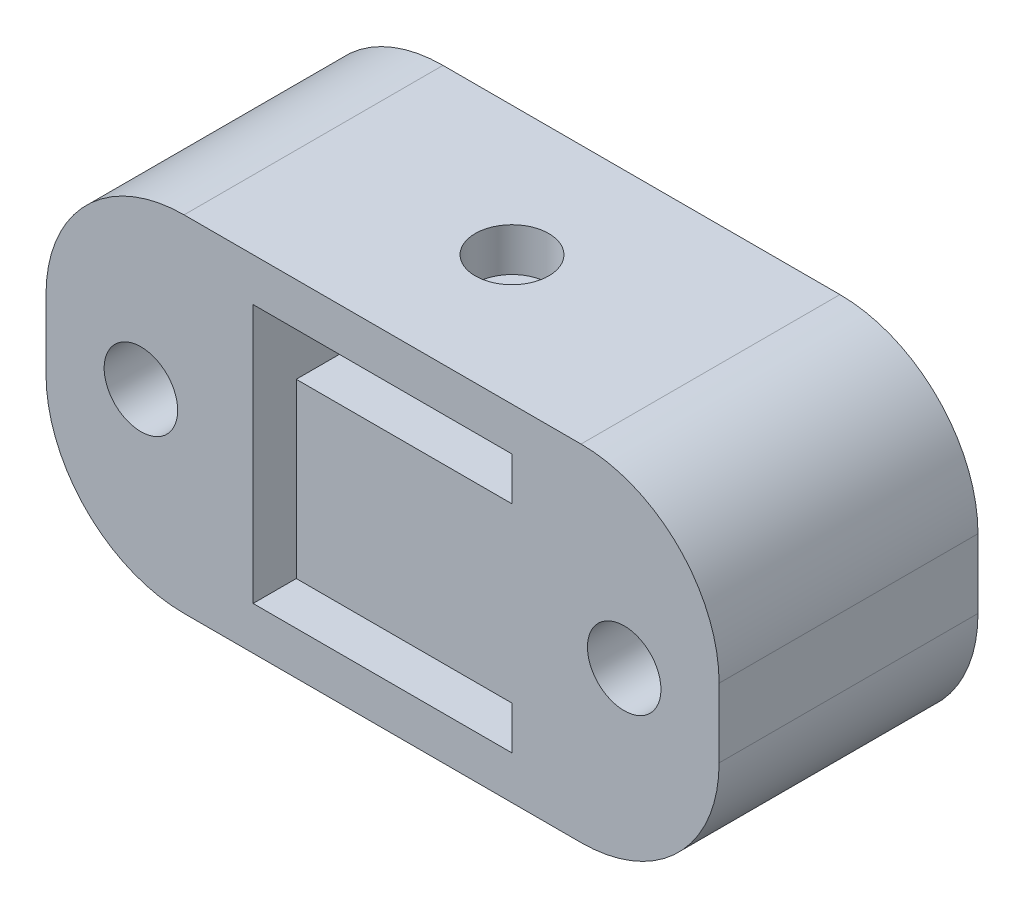
SolidWorks part; units mm, degrees
ref_plane "Front Plane" through (0, 0, 0) normal (0, 0, 1) x (1, 0, 0)
ref_plane "Top Plane" through (0, 0, 0) normal (0, 1, 0) x (1, 0, 0)
ref_plane "Right Plane" through (0, 0, 0) normal (1, 0, 0) x (0, 0, -1)
sketch "Sketch1" plane through (0, 0, 0) normal (0, 0, 1) x (1, 0, 0)
  line L1 (12.3825, -6.35) -> (-12.3825, -6.35)
  line L2 (12.3825, -6.35) -> (12.3825, 6.35)
  line L3 (12.3825, 6.35) -> (-12.3825, 6.35)
  line L4 (-12.3825, -6.35) -> (-12.3825, 6.35)
  line L5 (12.3825, -6.35) -> (-12.3825, 6.35) construction
  line L6 (12.3825, 6.35) -> (-12.3825, -6.35) construction
  point P0 (0, 0)
  dimension "D1" = 12.7
  dimension "D2" = 24.765
extrude "Boss-Extrude1" add sketch "Sketch1" along normal blind 9.525
sketch "Sketch2" plane through (0, 0, 9.525) normal (0, 0, 1) x (1, 0, 0)
  line L0 (4.7625, 4.7625) -> (-4.7625, 4.7625)
  line L1 (-4.7625, 4.7625) -> (-4.7625, -4.7625)
  line L2 (4.7625, 4.7625) -> (4.7625, 3.175)
  line L3 (4.7625, 3.175) -> (-3.175, 3.175)
  line L4 (-3.175, 3.175) -> (-3.175, -3.175)
  line L5 (0, 0) -> (8.6423, 0) construction
  line L6 (4.7625, -4.7625) -> (4.7625, -3.175)
  line L7 (4.7625, -3.175) -> (-3.175, -3.175)
  line L8 (4.7625, -4.7625) -> (-4.7625, -4.7625)
  point P3 (-3.175, 0)
  point P9 (0, 4.7625)
  point P14 (-4.7625, 0)
  dimension "D1" = 9.525
  dimension "D2" = 4.7625
  dimension "D3" = 1.5875
  dimension "D4" = 1.5875
extrude "Cut-Extrude1" cut sketch "Sketch2" against normal through all
fillet "Fillet1" radius 5.08 4 edges at (-12.3825, -6.35, 4.7625) (12.3825, -6.35, 4.7625) (12.3825, 6.35, 4.7625) (-12.3825, 6.35, 4.7625)
hole_wizard "#6-32 Tapped Hole2" positions "Sketch6" profile "Sketch3" tap size "#6-32" standard "ANSI Inch" end condition through all
sketch "Sketch6" plane through (0, 0, 9.525) normal (0, 0, 1) x (1, 0, 0)
  line L1 (0, 0) -> (0, 7.6794) construction
  point P0 (-8.89, 0)
  point P24 (8.89, 0)
  dimension "D1" = 8.89
sketch "Sketch3" plane through (-8.89, 0, 9.525) normal (1, 0, 0) x (0, -1, 0)
  line L0 (0, 0) -> (0, 9.525)
  line L1 (0, 9.525) -> (1.3525, 9.525)
  line L2 (1.3525, 9.525) -> (1.3525, 0)
  line L5 (1.3525, 0) -> (0, 0)
  line L11 (0, -6.35) -> (0, 107.95) construction
  dimension "Thread Major Dia." = 2.7051
  dimension "Thru Tap Drill Depth" = 9.525
hole_wizard "#6-32 Tapped Hole1" positions "Sketch8" profile "Sketch7" tap size "#6-32" standard "ANSI Inch"
sketch "Sketch8" plane through (0, 6.35, 0) normal (0, 1, 0) x (1, 0, 0)
  line L1 (7.3025, -9.525) -> (7.3025, 0) construction
  line L2 (7.3025, 0) -> (-7.3025, 0) construction
  point P0 (0, -4.7625)
  point P7 (7.3025, -4.7625)
  point P11 (0, 0)
sketch "Sketch7" plane through (0, 6.35, 4.7625) normal (1, 0, 0) x (0, 0, 1)
  line L0 (0, 0) -> (0, 11.176)
  line L1 (0, 11.176) -> (1.3525, 11.176)
  line L2 (1.3525, 11.176) -> (1.3525, 0)
  line L5 (1.3525, 0) -> (0, 0)
  line L10 (0, 11.176) -> (-1.3525, 11.176) construction
  line L11 (0, -6.35) -> (0, 107.95) construction
  dimension "Tap Drill Dia." = 2.7051
  dimension "Tap Drill Depth" = 11.176
  dimension "Drill Angle" = 180
cosmetic thread "Hole Thread1" parameters "D1"=7.112, "D2"=3.5052
